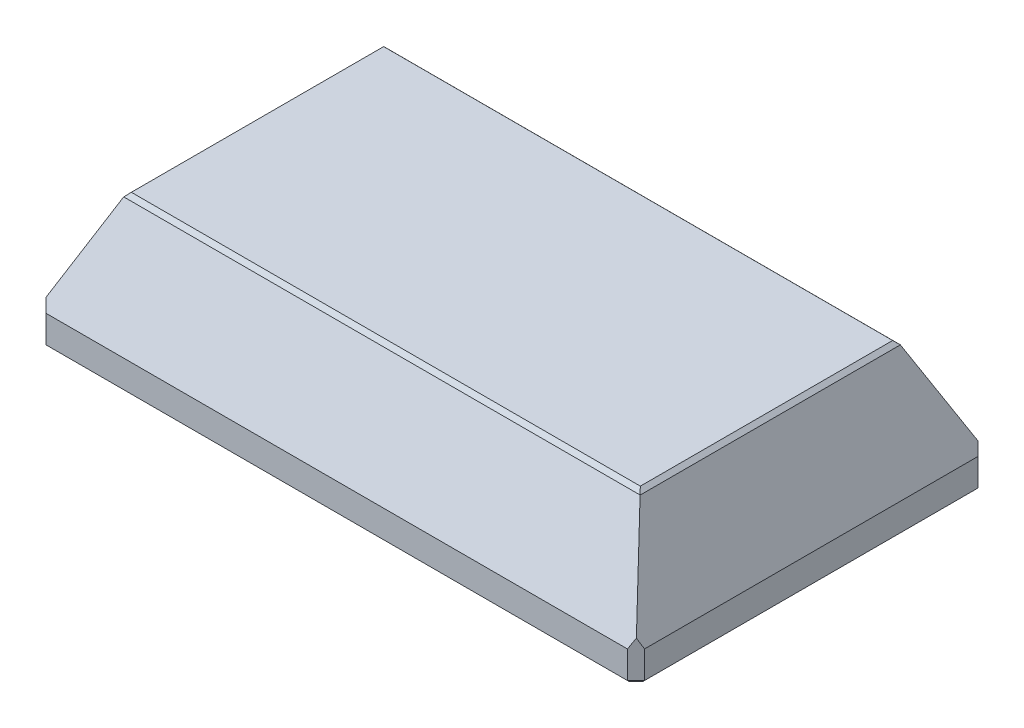
SolidWorks part; units mm, degrees
ref_plane "Front Plane" through (0, 0, 0) normal (0, 0, 1) x (1, 0, 0)
ref_plane "Top Plane" through (0, 0, 0) normal (0, 1, 0) x (1, 0, 0)
ref_plane "Right Plane" through (0, 0, 0) normal (1, 0, 0) x (0, 0, -1)
sketch "Sketch1" plane through (0, 0, 0) normal (0, 1, 0) x (1, 0, 0)
  line L1 (-70, -41) -> (70, -41)
  line L2 (-70, -41) -> (-70, 41)
  line L3 (-70, 41) -> (70, 41)
  line L4 (70, -41) -> (70, 41)
  line L5 (-70, -41) -> (70, 41) construction
  line L6 (-70, 41) -> (70, -41) construction
  point P0 (0, 0)
  dimension "D1" = 140
  dimension "D2" = 82
ref_plane "Plane1" through (0, 30, 0) normal (0, 1, 0) x (1, 0, 0)
sketch "Sketch2" plane through (0, 30, 0) normal (0, 1, 0) x (1, 0, 0)
  line L1 (-60, -30) -> (60, -30)
  line L2 (-60, -30) -> (-60, 30)
  line L3 (-60, 30) -> (60, 30)
  line L4 (60, -30) -> (60, 30)
  line L5 (-60, -30) -> (60, 30) construction
  line L6 (-60, 30) -> (60, -30) construction
  point P0 (0, 0)
  dimension "D1" = 60
  dimension "D2" = 120
extrude "Boss-Extrude1" add sketch "Sketch1" along normal blind 7
sketch "Sketch3" plane through (0, 7, 0) normal (0, 1, 0) x (1, 0, 0)
  line L4 (70, -41) -> (70, 41)
  line L5 (70, 41) -> (-70, 41)
  line L6 (-70, 41) -> (-70, -41)
  line L7 (-70, -41) -> (70, -41)
  line L8 (70, -41) -> (70, 41)
  line L9 (70, 41) -> (-70, 41)
  line L10 (-70, 41) -> (-70, -41)
  line L11 (-70, -41) -> (70, -41)
  dimension "D1" = 0
loft "Loft2" add profiles "Sketch3", "Sketch2"
chamfer "Chamfer1" distance 2 angle 45 4 edges at (-70, 3.5, 41) (70, 3.5, 41) (70, 3.5, -41) (-70, 3.5, -41)
sketch "Sketch4" plane through (0, 0, 0) normal (0, -1, 0) x (1, 0, 0)
  line L0 (0, 41) -> (0, -41) construction
  line L1 (-68, 41) -> (68, 41) construction
  line L2 (68, -41) -> (-68, -41) construction
  line L3 (-40, -37.5) -> (40, -37.5) construction
  circle A0 centre (40, -37.5) radius 2.05
  circle A1 centre (-40, -37.5) radius 2.05
  point P9 (0, -37.5)
  dimension "D3" = 4.1
  dimension "D1" = 3.5
  dimension "D2" = 80
extrude "Cut-Extrude1" cut sketch "Sketch4" against normal blind 7
sketch "Sketch5" plane through (0, 0, 0) normal (0, -1, 0) x (1, 0, 0)
  line L1 (-57, -25) -> (57, -25)
  line L2 (-57, -25) -> (-57, 25)
  line L3 (-57, 25) -> (57, 25)
  line L4 (57, -25) -> (57, 25)
  line L5 (-57, -25) -> (57, 25) construction
  line L6 (-57, 25) -> (57, -25) construction
  point P0 (0, 0)
  dimension "D1" = 50
  dimension "D2" = 114
extrude "Cut-Extrude2" cut sketch "Sketch5" against normal offset from surface (29 mm away) 1 up to face at (0, 30, 0)
mirror "Mirror1" about plane through (0, 0, 0) normal (0, 0, 1) of "Cut-Extrude1"
sketch "Sketch6" plane through (0, 0, 0) normal (0, -1, 0) x (1, 0, 0)
  line L0 (57, 25) -> (57, -25) construction
  line L1 (-57, -31) -> (57, -31)
  line L2 (-57, -31) -> (-57, 31)
  line L3 (-57, 31) -> (57, 31)
  line L4 (57, -31) -> (57, 31)
  line L5 (-57, -31) -> (57, 31) construction
  line L6 (-57, 31) -> (57, -31) construction
  line L7 (57, 25) -> (-57, 25) construction
  point P0 (0, 0)
  dimension "D1" = 6
extrude "Cut-Extrude3" cut sketch "Sketch6" against normal offset from surface (25 mm away) 4 up to face at (0, 29, 0)
sketch "Sketch7" plane through (0, 0, 0) normal (0, -1, 0) x (1, 0, 0)
  line L0 (-57, -31) -> (57, -31) construction
  line L1 (-57, 31) -> (-63, 31)
  line L2 (-57, 31) -> (-57, -31)
  line L3 (-57, -31) -> (-63, -31)
  line L4 (-63, 31) -> (-63, -31)
  line L5 (0, 41) -> (0, -41) construction
  line L6 (-68, 41) -> (68, 41) construction
  line L7 (68, -41) -> (-68, -41) construction
  line L8 (63, 31) -> (63, -31)
  line L9 (57, -31) -> (63, -31)
  line L10 (57, 31) -> (57, -31)
  line L11 (57, 31) -> (63, 31)
  dimension "D1" = 6
extrude "Cut-Extrude4" cut sketch "Sketch7" against normal blind 4
sketch "Sketch8" plane through (0, 4, 0) normal (0, -1, 0) x (1, 0, 0)
  line L0 (-63, 0) -> (63, 0) construction
  line L1 (-63, 31) -> (-63, -31) construction
  line L2 (63, -31) -> (63, 31) construction
  line L3 (-60, -25) -> (-60, 25) construction
  line L4 (-63, 31) -> (-57, -31) construction
  line L5 (0, 31) -> (0, -31) construction
  line L6 (-57, 31) -> (57, 31) construction
  line L7 (-63, -31) -> (63, -31) construction
  circle A0 centre (-60, 25) radius 2.05
  circle A1 centre (-60, -25) radius 2.05
  circle A2 centre (60, -25) radius 2.05
  circle A3 centre (60, 25) radius 2.05
  point P9 (-60, 0)
  dimension "D1" = 4.1
  dimension "D2" = 50
extrude "Cut-Extrude5" cut sketch "Sketch8" against normal blind 6
chamfer "Chamfer2" distance 1 angle 20 4 edges
chamfer "Chamfer3" distance 0.6 angle 45 8 edges at (69, 0, -40) (70, 0, 0) (69, 0, 40) (0, 0, -41) (-69, 0, -40) (-70, 0, 0) (-69, 0, 40) (0, 0, 41)
sketch "Skizze1" plane through (0, 29, 0) normal (0, -1, 0) x (1, 0, 0)
  line L0 (0, 25) -> (0, -25) construction
  line L1 (-57, 25) -> (57, 25) construction
  line L2 (-57, 25) -> (57, 25) construction
  line L3 (57, 0) -> (-57, 0) construction
  line L4 (57, 25) -> (57, -25) construction
  line L5 (-57, -31) -> (-57, 31) construction
  line L6 (-27.0252, -17.5) -> (27.0252, -17.5)
  line L7 (-27.0252, 25) -> (27.0252, 25)
  line L8 (-27.0252, 25) -> (-27.0252, 17.5)
  line L9 (-27.0252, 17.5) -> (27.0252, 17.5)
  line L10 (27.0252, 25) -> (27.0252, 17.5)
  line L11 (27.0252, -25) -> (27.0252, -17.5)
  line L12 (-27.0252, -25) -> (27.0252, -25)
  line L13 (-27.0252, -25) -> (-27.0252, -17.5)
  line L14 (57, 31) -> (57, -31) construction
  line L15 (57, 10.7265) -> (53, 10.7265)
  line L16 (57, 10.7265) -> (57, -10.7265)
  line L17 (57, -10.7265) -> (53, -10.7265)
  line L18 (53, 10.7265) -> (53, -10.7265)
  line L23 (-57, -25) -> (-57, 25) construction
  point P29 (0, 17.5)
  dimension "D1" = 35
  dimension "D2" = 110
extrude "Aufsatz-Linear austragen1" add sketch "Skizze1" along normal blind 10
sketch "Skizze3" plane through (0, 29, 0) normal (0, -1, 0) x (-1, 0, 0)
  line L0 (57, -25) -> (57, -31) construction
  line L2 (57, -28) -> (57, -25)
  line L10 (27.0252, -25) -> (27.0252, -28)
  line L11 (27.0252, -28) -> (57, -28)
  line L12 (27.0252, -25) -> (57, -25)
  line L14 (0, -40.4) -> (0, 40.4) construction
  line L22 (-67.7515, -40.4) -> (67.7515, -40.4) construction
  line L23 (67.7515, 40.4) -> (-67.7515, 40.4) construction
  line L24 (69.4, 0) -> (-69.4, 0) construction
  line L25 (69.4, -38.7515) -> (69.4, 38.7515) construction
  line L26 (-69.4, 38.7515) -> (-69.4, -38.7515) construction
  line L27 (-27.0252, -25) -> (-27.0252, -28)
  line L28 (-27.0252, -25) -> (-57, -25)
  line L29 (-27.0252, -28) -> (-57, -28)
  line L30 (-57, -28) -> (-57, -25)
  line L31 (27.0252, 25) -> (27.0252, 28)
  line L32 (27.0252, 28) -> (57, 28)
  line L33 (27.0252, 25) -> (57, 25)
  line L34 (57, 28) -> (57, 25)
  line L35 (-57, 28) -> (-57, 25)
  line L36 (-27.0252, 28) -> (-57, 28)
  line L37 (-27.0252, 25) -> (-27.0252, 28)
  line L38 (-27.0252, 25) -> (-57, 25)
extrude "Schnitt-Linear austragen2" cut sketch "Skizze3" along normal up to surface (4 mm away) up to face at (0, 25, 27)
